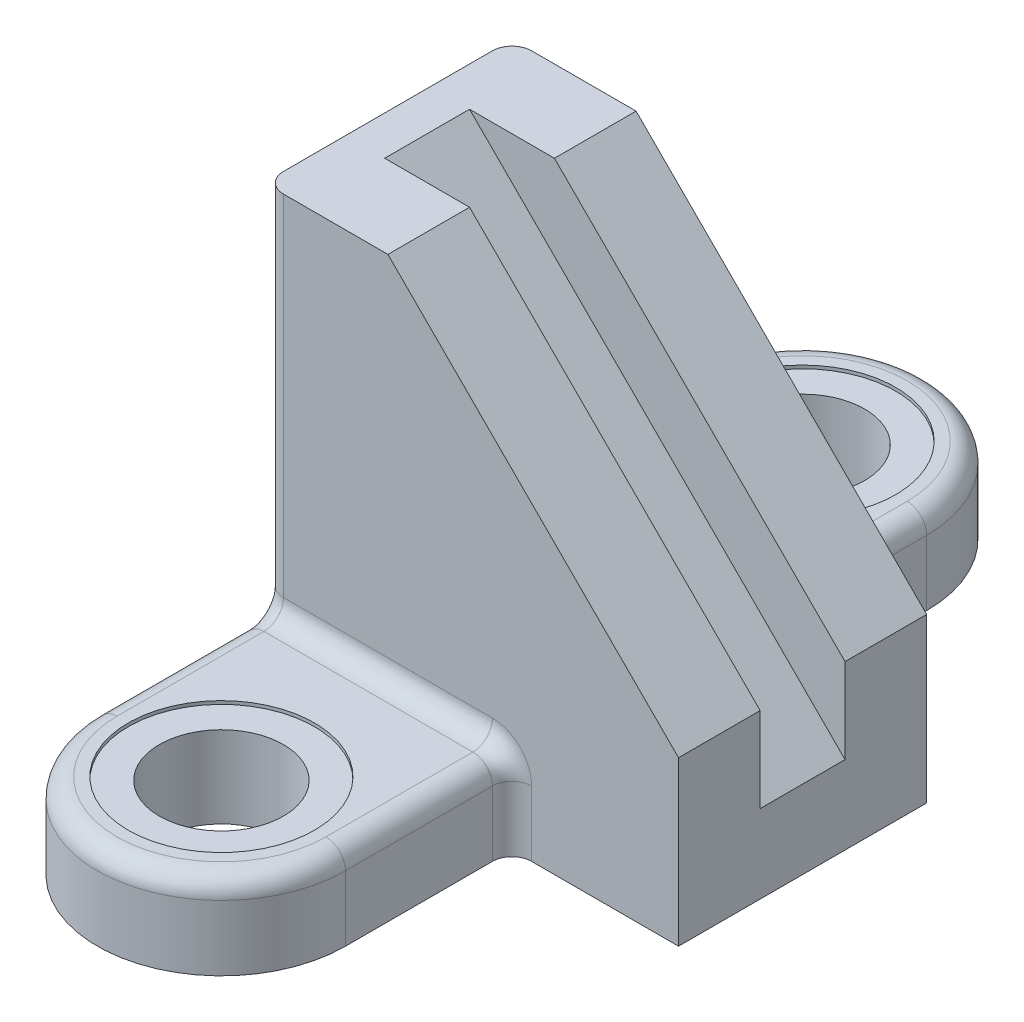
SolidWorks part; units mm, degrees
material "2014 Alloy"
ref_plane "Front Plane" through (0, 0, 0) normal (0, 0, 1) x (1, 0, 0)
ref_plane "Top Plane" through (0, 0, 0) normal (0, 1, 0) x (1, 0, 0)
ref_plane "Right Plane" through (0, 0, 0) normal (1, 0, 0) x (0, 0, -1)
sketch "Sketch1" plane through (0, 0, 0) normal (0, 0, 1) x (1, 0, 0)
  line L0 (38, 139) -> (127, 50)
  line L1 (0, 0) -> (127, 0)
  line L2 (0, 0) -> (0, 139)
  line L3 (0, 139) -> (38, 139)
  line L4 (127, 0) -> (127, 50)
  line L5 (127, 50) -> (67.3806, 50) construction
  dimension "D1" = 127
  dimension "D2" = 45
  dimension "D3" = 50
  dimension "D4" = 38
extrude "Boss-Extrude1" add sketch "Sketch1" along normal mid plane 76
sketch "Sketch3" plane through (0, 0, 0) normal (0, 1, 0) x (1, 0, 0)
  line L0 (0, 0) -> (116.7501, 0) construction
  line L1 (0, 38) -> (76, 38)
  line L2 (0, 38) -> (0, 89)
  line L4 (76, 38) -> (76, 89)
  line L9 (0, -38) -> (76, -38)
  line L10 (76, -38) -> (76, -89)
  line L11 (0, -38) -> (0, -89)
  arc A0 (0, 89) -> (76, 89) centre (38, 89) cw
  arc A1 (0, -89) -> (76, -89) centre (38, -89) ccw
  dimension "D1" = 89
  dimension "D2" = 76
extrude "Boss-Extrude3" add sketch "Sketch3" along normal blind 26
fillet "Fillet1" radius 6 12 edges at (76, 13, -38) (76, 13, 38) (76, 26, -63.5) (0, 26, -63.5) (76, 26, 63.5) (38, 26, 127) (38, 26, -127) (0, 82.5, -38) (38, 26, -38) (38, 26, 38) (0, 26, 63.5) (0, 82.5, 38)
hole_wizard "CBORE for M30 Hex Head Bolt2" positions "Sketch11" profile "Sketch12" counterbore size "M30" standard "ANSI Metric" end condition through all
sketch "Sketch11" plane through (0, 26, 0) normal (0, 1, 0) x (1, 0, 0)
  point P0 (38, -89)
  point P3 (38, 89)
sketch "Sketch12" plane through (38, 26, 89) normal (1, 0, 0) x (0, 0, 1)
  line L0 (0, 0) -> (0, 26)
  line L1 (0, 26) -> (19, 26)
  line L3 (19, 26) -> (19, 1)
  line L4 (19, 1) -> (28.5, 1)
  line L5 (28.5, 1) -> (28.5, 0)
  line L7 (28.5, 0) -> (0, 0)
  line L11 (0, -6.35) -> (0, 107.95) construction
  dimension "Thru Hole Dia." = 38
  dimension "Thru Hole Depth" = 26
  dimension "C'Bore Dia." = 57
  dimension "C'Bore Depth" = 1
sketch "Sketch16" plane through (0, 139, 0) normal (0, 1, 0) x (1, 0, 0)
  line L0 (12, -38) -> (12, 38) construction
  line L1 (38, -38) -> (6, -38) construction
  line L2 (38, 38) -> (6, 38) construction
  line L3 (0, -32) -> (0, 32) construction
  dimension "D1" = 12
ref_plane "Plane3" through (-63.5, 63.5, 0) normal (-0.7071, 0.7071, 0) x (0, 0, -1)
sketch "Sketch17" plane through (-63.5, 63.5, 0) normal (-0.7071, 0.7071, 0) x (0, 0, -1)
  line L0 (-38, -106.7731) -> (38, -106.7731) construction
  line L1 (-13, -106.7731) -> (13, -106.7731)
  line L2 (-13, -106.7731) -> (-13, -125.1579)
  line L3 (-13, -125.1579) -> (13, -125.1579)
  line L4 (13, -106.7731) -> (13, -125.1579)
  line L5 (-38, -125.1579) -> (38, -125.1579) construction
  point P8 (0, -106.7731)
  dimension "D1" = 26
extrude "Cut-Extrude3" cut sketch "Sketch17" against normal through all
